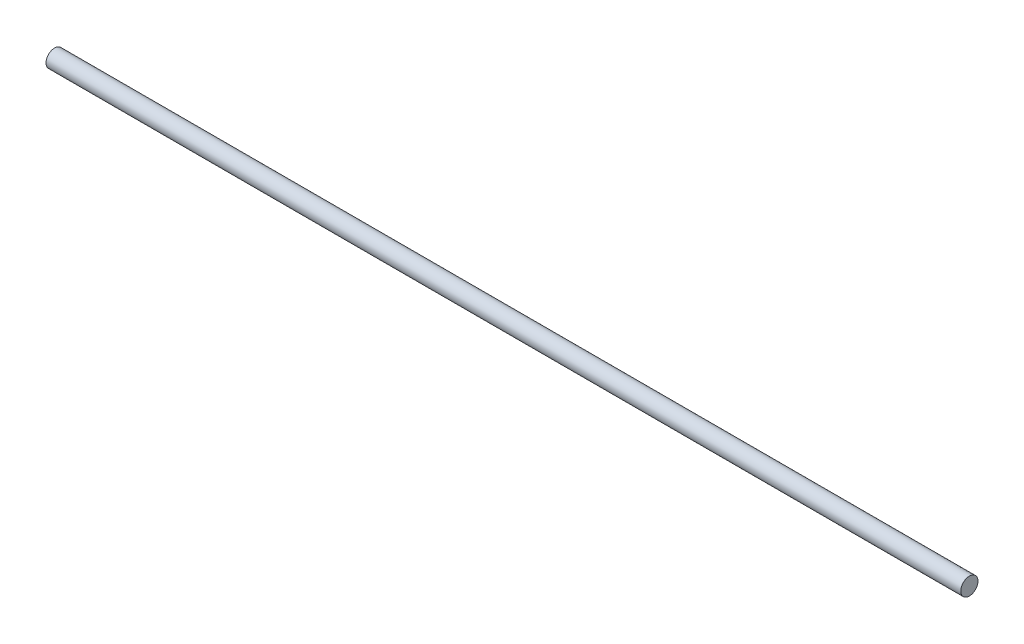
SolidWorks part; units mm, degrees
ref_plane "Front Plane" through (0, 0, 0) normal (0, 0, 1) x (1, 0, 0)
ref_plane "Top Plane" through (0, 0, 0) normal (0, 1, 0) x (1, 0, 0)
ref_plane "Right Plane" through (0, 0, 0) normal (1, 0, 0) x (0, 0, -1)
sketch "Sketch1" plane through (0, 0, 0) normal (1, 0, 0) x (0, 0, -1)
  circle A0 centre (0, 0) radius 0.003
  circle A1 centre (0, 0) radius 3
extrude "Boss-Extrude1" add sketch "Sketch1" along normal mid plane 318
